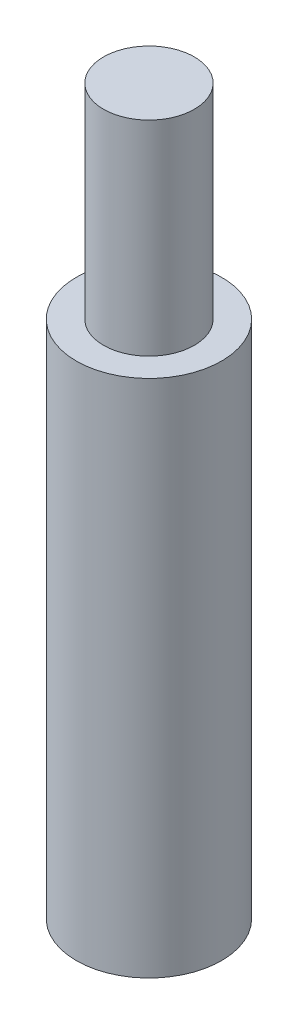
SolidWorks part; units mm, degrees
ref_plane "Front Plane" through (0, 0, 0) normal (0, 0, 1) x (1, 0, 0)
ref_plane "Top Plane" through (0, 0, 0) normal (0, 1, 0) x (1, 0, 0)
ref_plane "Right Plane" through (0, 0, 0) normal (1, 0, 0) x (0, 0, -1)
sketch "Sketch1" plane through (0, 0, 0) normal (0, 1, 0) x (1, 0, 0)
  circle A0 centre (0, 0) radius 5.08
  dimension "D1" = 10.16
extrude "Boss-Extrude1" add sketch "Sketch1" along normal blind 50.62
sketch "Sketch2" plane through (0, 50.62, 0) normal (0, 1, 0) x (1, 0, 0)
  circle A0 centre (0, 0) radius 3.175
  circle A2 centre (0, 0) radius 5.08
  circle A3 centre (0, 0) radius 5.08
  dimension "D2" = 6.35
  dimension "D1" = 0
extrude "Cut-Extrude1" cut sketch "Sketch2" against normal blind 14.3
